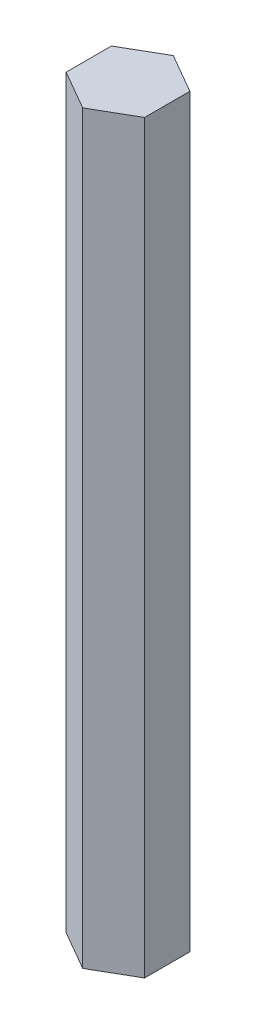
SolidWorks part; units mm, degrees
ref_plane "Front Plane" through (0, 0, 0) normal (0, 0, 1) x (1, 0, 0)
ref_plane "Top Plane" through (0, 0, 0) normal (0, 1, 0) x (1, 0, 0)
ref_plane "Right Plane" through (0, 0, 0) normal (1, 0, 0) x (0, 0, -1)
sketch "Sketch1" plane through (0, 0, 0) normal (0, 1, 0) x (1, 0, 0)
  line L1 (0, 7.3323) -> (-6.35, 3.6662)
  line L2 (-6.35, 3.6662) -> (-6.35, -3.6662)
  line L3 (-6.35, -3.6662) -> (0, -7.3323)
  line L4 (0, -7.3323) -> (6.35, -3.6662)
  line L5 (6.35, -3.6662) -> (6.35, 3.6662)
  line L6 (6.35, 3.6662) -> (0, 7.3323)
  circle A0 centre (0, 0) radius 6.35 construction
  circle A1 centre (0, 0) radius 2.5527 construction
  dimension "D2" = 5.1054
  dimension "D1" = 12.7
extrude "Boss-Extrude1" add sketch "Sketch1" along normal blind 120.65
hole_wizard "#10-32 Tapped Hole1" positions "3DSketch1" profile "Sketch3" tap size "#10-32" standard "ANSI Inch"
sketch3d "3DSketch1"
  point P11 (0, 0, 0)
sketch "Sketch3" plane through (0, 0, 0) normal (1, 0, 0) x (0, 0, -1)
  line L0 (0, 0) -> (0, 17.9773)
  line L1 (0, 17.9773) -> (2.0193, 16.764)
  line L2 (2.0193, 16.764) -> (2.0193, 12.7)
  line L3 (2.0193, 12.7) -> (2.413, 12.7)
  line L4 (2.413, 12.7) -> (2.413, 0)
  line L5 (2.413, 0) -> (0, 0)
  line L10 (0, 17.9773) -> (-2.0193, 16.764) construction
  line L11 (0, -6.35) -> (0, 107.95) construction
  dimension "Tap Drill Dia." = 4.0386
  dimension "Tap Drill Depth" = 16.764
  dimension "Thread Major Dia." = 4.826
  dimension "Thread Depth" = 12.7
  dimension "Drill Angle" = 118
